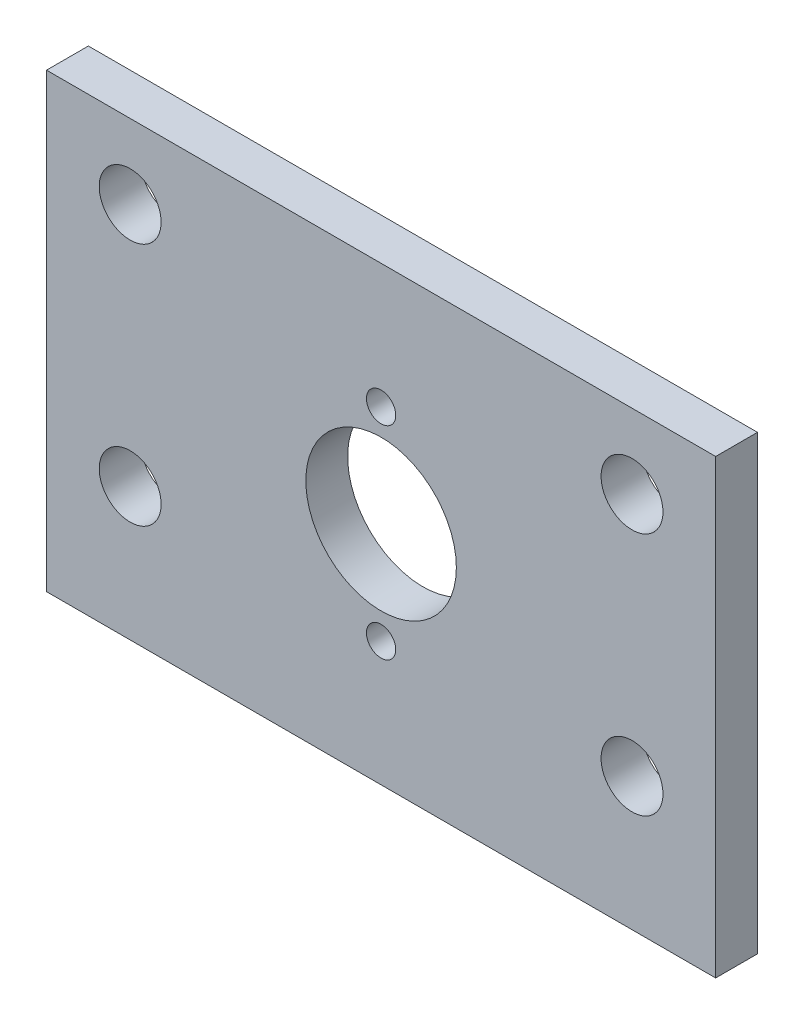
SolidWorks part; units mm, degrees
ref_plane "Front Plane" through (0, 0, 0) normal (0, 0, 1) x (1, 0, 0)
ref_plane "Top Plane" through (0, 0, 0) normal (0, 1, 0) x (1, 0, 0)
ref_plane "Right Plane" through (0, 0, 0) normal (1, 0, 0) x (0, 0, -1)
sketch "Sketch1" plane through (0, 0, 0) normal (0, 0, 1) x (1, 0, 0)
  line L0 (0, 7.7025) -> (0, -7.7025) construction
  line L1 (-25.4, -17.145) -> (25.4, -17.145)
  line L2 (-25.4, -17.145) -> (-25.4, 17.145)
  line L3 (-25.4, 17.145) -> (25.4, 17.145)
  line L4 (25.4, -17.145) -> (25.4, 17.145)
  line L5 (-25.4, -17.145) -> (25.4, 17.145) construction
  line L6 (-25.4, 17.145) -> (25.4, -17.145) construction
  line L7 (-25.4, -7.0485) -> (-21.3995, -7.0485) construction
  line L9 (19.05, -7.0485) -> (19.05, -17.145) construction
  line L10 (21.3995, -7.0485) -> (25.4, -7.0485) construction
  circle A0 centre (19.05, -7.0485) radius 2.3495
  circle A1 centre (19.05, 11.4935) radius 2.3495
  circle A2 centre (-19.05, 11.4935) radius 2.3495
  circle A3 centre (-19.05, -7.0485) radius 2.3495
  circle A4 centre (0, 7.7025) radius 1.1112
  circle A5 centre (0, -7.7025) radius 1.1112
  circle A6 centre (0, 0) radius 5.715
  point P0 (0, 0)
  point P20 (0, 0)
  dimension "D1" = 4.699
  dimension "D2" = 18.542
  dimension "D9" = 2.2225
  dimension "D10" = 11.43
  dimension "D3" = 50.8
  dimension "D4" = 34.29
  dimension "D5" = 4.0005
  dimension "D6" = 10.0965
  dimension "D8" = 15.4051
extrude "Boss-Extrude1" add sketch "Sketch1" along normal blind 3.175
